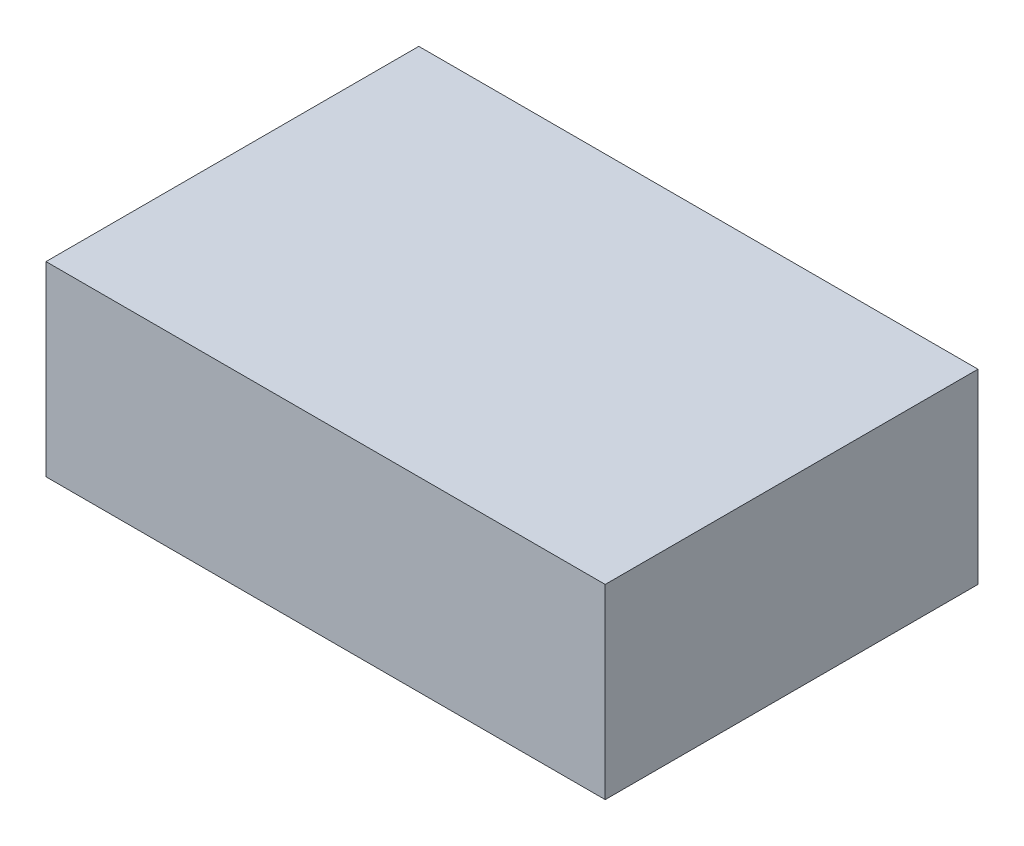
SolidWorks part; units mm, degrees
material "ABS"
ref_plane "Front Plane" through (0, 0, 0) normal (0, 0, 1) x (1, 0, 0)
ref_plane "Top Plane" through (0, 0, 0) normal (0, 1, 0) x (1, 0, 0)
ref_plane "Right Plane" through (0, 0, 0) normal (1, 0, 0) x (0, 0, -1)
sketch "Sketch2" plane through (0, 0, 0) normal (0, 1, 0) x (1, 0, 0)
  line L1 (76.2, -50.8) -> (-76.2, -50.8)
  line L2 (76.2, -50.8) -> (76.2, 50.8)
  line L3 (76.2, 50.8) -> (-76.2, 50.8)
  line L4 (-76.2, -50.8) -> (-76.2, 50.8)
  line L5 (76.2, -50.8) -> (-76.2, 50.8) construction
  line L6 (76.2, 50.8) -> (-76.2, -50.8) construction
  point P0 (0, 0)
  dimension "D1" = 152.4
  dimension "D2" = 101.6
extrude "Boss-Extrude1" add sketch "Sketch2" along normal mid plane 50.8
